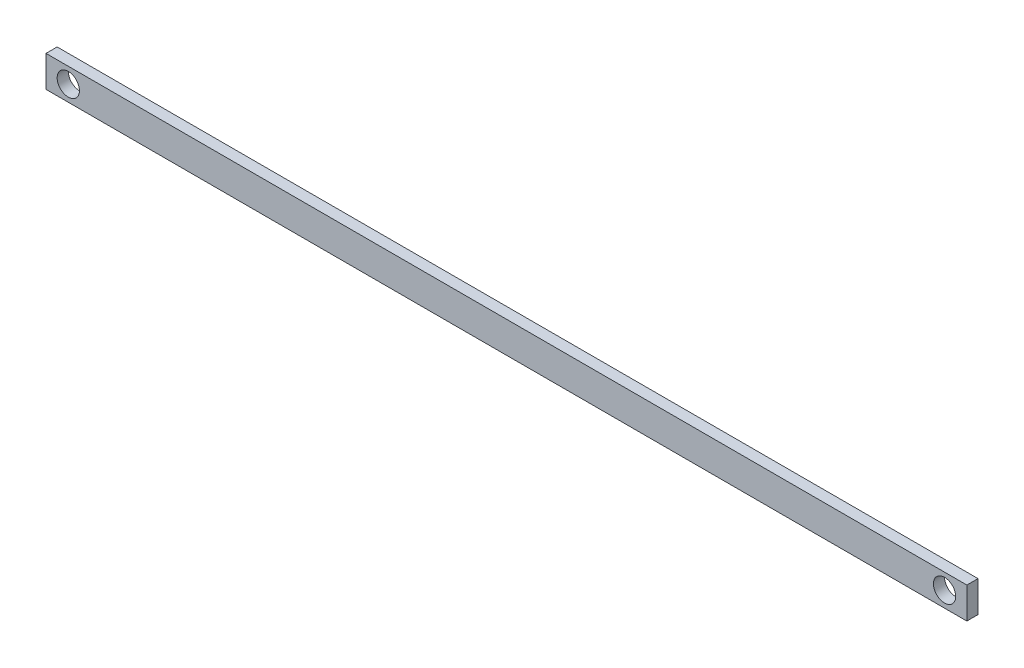
SolidWorks part; units mm, degrees
ref_plane "Front Plane" through (0, 0, 0) normal (0, 0, 1) x (1, 0, 0)
ref_plane "Top Plane" through (0, 0, 0) normal (0, 1, 0) x (1, 0, 0)
ref_plane "Right Plane" through (0, 0, 0) normal (1, 0, 0) x (0, 0, -1)
sketch "Sketch1" plane through (0, 0, 0) normal (0, 0, 1) x (1, 0, 0)
  line L0 (0, 0) -> (0, 140)
  line L1 (0, 140) -> (3930, 140)
  line L2 (3930, 140) -> (3930, 0)
  line L3 (3930, 0) -> (0, 0)
  dimension "D1" = 3930
  dimension "D2" = 140
extrude "Boss-Extrude1" add sketch "Sketch1" along normal blind 50
sketch "Sketch2" plane through (0, 0, 50) normal (0, 0, 1) x (1, 0, 0)
  line L0 (3930, 0) -> (3930, 140) construction
  line L1 (0, 140) -> (0, 0) construction
  circle A0 centre (3930, 70) radius 50
  circle A1 centre (0, 70) radius 50
  dimension "D1" = 100
  dimension "D2" = 100
extrude "Cut-Extrude1" cut sketch "Sketch2" against normal blind 50
sketch "Sketch3" plane through (0, 0, 0) normal (0, 0, -1) x (-1, 0, 0)
  line L0 (-3930, 140) -> (-4030, 140)
  line L1 (-4030, 140) -> (-4030, 0)
  line L2 (-4030, 0) -> (-3930, 0)
  line L3 (-3930, 0) -> (-3930, 140)
  line L4 (0, 140) -> (100, 140)
  line L5 (100, 140) -> (100, 0)
  line L6 (100, 0) -> (0, 0)
  line L7 (0, 0) -> (0, 140)
  dimension "D1" = 100
  dimension "D2" = 100
extrude "Boss-Extrude2" add sketch "Sketch3" against normal through all
sketch "Sketch4" plane through (0, 0, 0) normal (0, 0, -1) x (-1, 0, 0)
  line L0 (0, 120) -> (0, 20) construction
  line L1 (-3930, 20) -> (-3930, 120) construction
  circle A0 centre (0, 70) radius 50
  circle A1 centre (-3930, 70) radius 50
extrude "Cut-Extrude2" cut sketch "Sketch4" against normal through all
